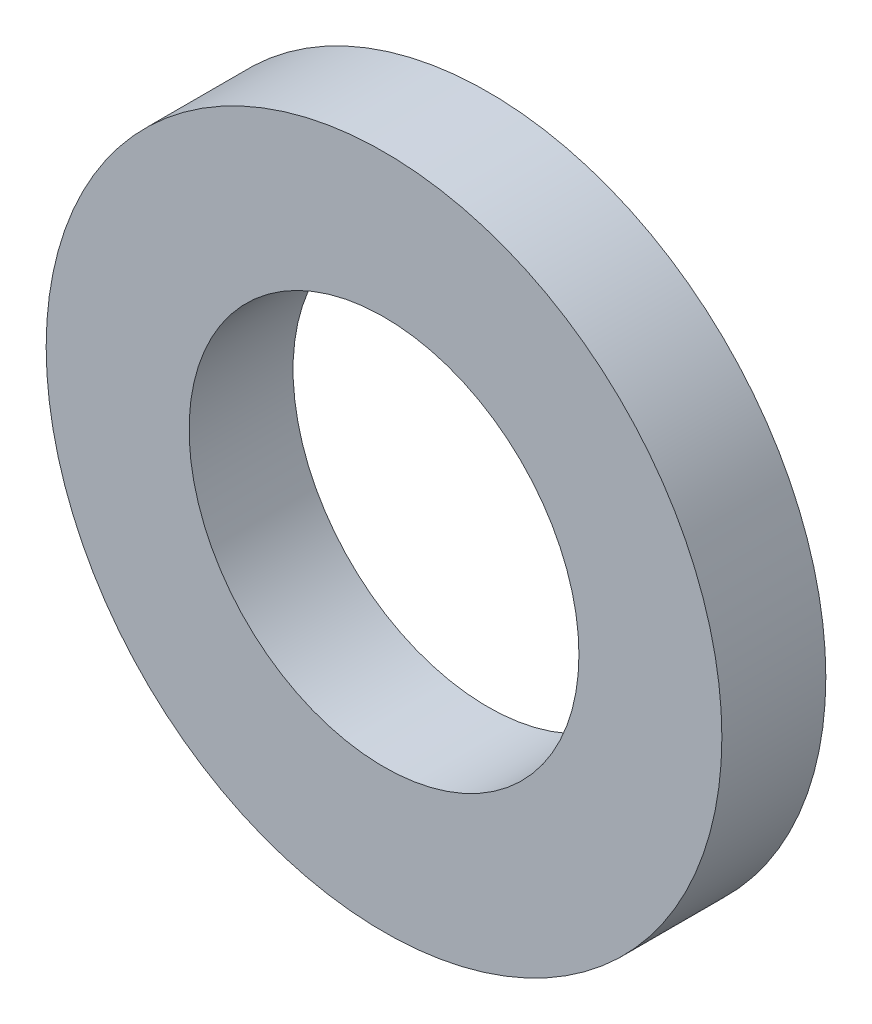
SolidWorks part; units mm, degrees
material "PVC Rigid"
ref_plane "Front Plane" through (0, 0, 0) normal (0, 0, 1) x (1, 0, 0)
ref_plane "Top Plane" through (0, 0, 0) normal (0, 1, 0) x (1, 0, 0)
ref_plane "Right Plane" through (0, 0, 0) normal (1, 0, 0) x (0, 0, -1)
sketch "Sketch1" plane through (0, 0, 0) normal (0, 0, 1) x (1, 0, 0)
  circle A0 centre (0, 0) radius 7.5
  circle A1 centre (0, 0) radius 13
  dimension "D1" = 15
  dimension "D2" = 26
extrude "Boss-Extrude1" add sketch "Sketch1" along normal blind 4
